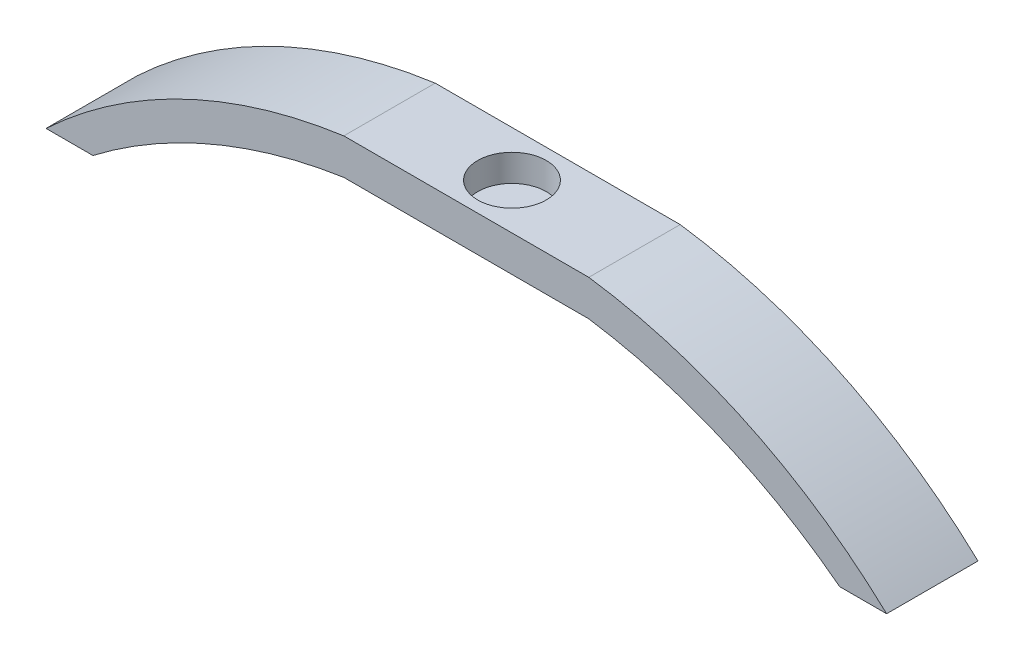
SolidWorks part; units mm, degrees
ref_plane "Front Plane" through (0, 0, 0) normal (0, 0, 1) x (1, 0, 0)
ref_plane "Top Plane" through (0, 0, 0) normal (0, 1, 0) x (1, 0, 0)
ref_plane "Right Plane" through (0, 0, 0) normal (1, 0, 0) x (0, 0, -1)
sketch "Sketch1" plane through (0, 0, 0) normal (0, 1, 0) x (1, 0, 0)
  line L1 (-7.62, 5.08) -> (7.62, 5.08)
  line L2 (-7.62, 5.08) -> (-7.62, -5.08)
  line L3 (-7.62, -5.08) -> (7.62, -5.08)
  line L4 (7.62, 5.08) -> (7.62, -5.08)
  line L5 (-7.62, 5.08) -> (7.62, -5.08) construction
  line L6 (-7.62, -5.08) -> (7.62, 5.08) construction
  point P0 (0, 0)
  dimension "D1" = 15.24
  dimension "D2" = 10.16
extrude "Boss-Extrude1" add sketch "Sketch1" along normal blind 4
sketch "Sketch2" plane through (0, 4, 0) normal (0, 1, 0) x (1, 0, 0)
  circle A0 centre (0, 0) radius 3.81
  dimension "D1" = 7.62
extrude "Cut-Extrude1" cut sketch "Sketch2" against normal blind 3
sketch "Sketch3" plane through (0, 0, 5.08) normal (0, 0, 1) x (1, 0, 0)
  line L0 (0, 4) -> (0, -11.84) construction
  line L1 (-7.62, 4) -> (7.62, 4) construction
  line L2 (7.62, 4) -> (7.62, -55.35) construction
  line L3 (0, -11.84) -> (7.62, -11.84)
  line L4 (7.62, 4) -> (13.62, 4)
  line L5 (46.735, -11.84) -> (41.515, -11.84)
  line L6 (41.515, -11.84) -> (46.735, -11.84)
  line L7 (7.62, 4) -> (7.62, 0)
  line L8 (7.62, 0) -> (13.62, 0)
  line L9 (-46.735, -11.84) -> (-41.515, -11.84)
  line L10 (-7.62, 4) -> (-7.62, 0)
  line L11 (-7.62, 0) -> (-13.62, 0)
  line L12 (-7.62, 4) -> (-13.62, 4)
  arc A2 (41.515, -11.84) -> (13.62, 0) centre (4.6546, -59.9028) ccw
  arc A3 (-41.515, -11.84) -> (-13.62, 0) centre (-4.6546, -59.9028) cw
  arc A4 (-46.735, -11.84) -> (-13.62, 4) centre (-5.2699, -55.9917) cw
  arc A5 (46.735, -11.84) -> (13.62, 4) centre (5.2699, -55.9917) ccw
  dimension "D2" = 6
  dimension "D3" = 121.14
  dimension "D5" = 121.14
  dimension "D1" = 15.84
  dimension "D4" = 5.22
extrude "Boss-Extrude2" add sketch "Sketch3" against normal up to surface (10.16 mm away) up to face at (0, 2, -5.08)
